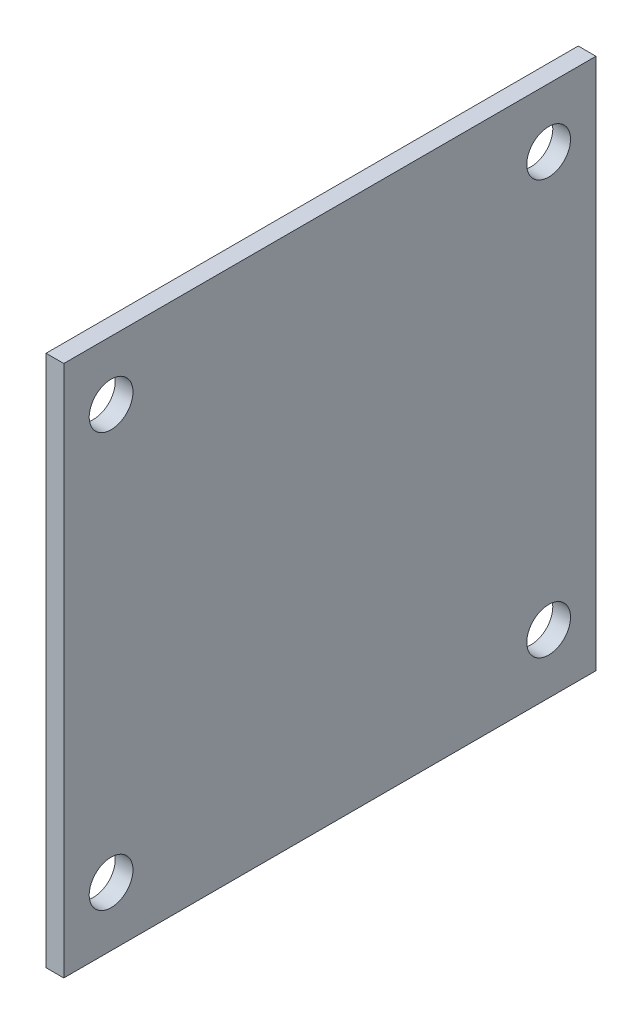
SolidWorks part; units mm, degrees
ref_plane "Front Plane" through (0, 0, 0) normal (0, 0, 1) x (1, 0, 0)
ref_plane "Top Plane" through (0, 0, 0) normal (0, 1, 0) x (1, 0, 0)
ref_plane "Right Plane" through (0, 0, 0) normal (1, 0, 0) x (0, 0, -1)
sketch "Sketch1" plane through (0, 0, 0) normal (1, 0, 0) x (0, 0, -1)
  line L1 (-22.5, -22.5) -> (22.5, -22.5)
  line L2 (-22.5, -22.5) -> (-22.5, 22.5)
  line L3 (-22.5, 22.5) -> (22.5, 22.5)
  line L4 (22.5, -22.5) -> (22.5, 22.5)
  line L5 (-22.5, -22.5) -> (22.5, 22.5) construction
  line L6 (-22.5, 22.5) -> (22.5, -22.5) construction
  point P0 (0, 0)
  dimension "D1" = 45
  dimension "D2" = 45
extrude "Boss-Extrude1" add sketch "Sketch1" along normal blind 1.5
sketch "Sketch2" plane through (1.5, 0, 0) normal (1, 0, 0) x (0, 0, -1)
  line L0 (22.5, -22.5) -> (22.5, 22.5) construction
  line L1 (-22.5, -22.5) -> (22.5, -22.5) construction
  circle A0 centre (-18.5, 17.5) radius 1.85
  circle A1 centre (-18.5, -17.5) radius 1.85
  circle A2 centre (18.5, 17.5) radius 1.85
  circle A3 centre (18.5, -17.5) radius 1.85
  dimension "D6" = 3.7
  dimension "D7" = 3.7
  dimension "D8" = 3.7
  dimension "D9" = 3.7
  dimension "D1" = 35
  dimension "D2" = 35
  dimension "D3" = 37
  dimension "D4" = 4
  dimension "D5" = 5
extrude "Cut-Extrude1" cut sketch "Sketch2" against normal through all
